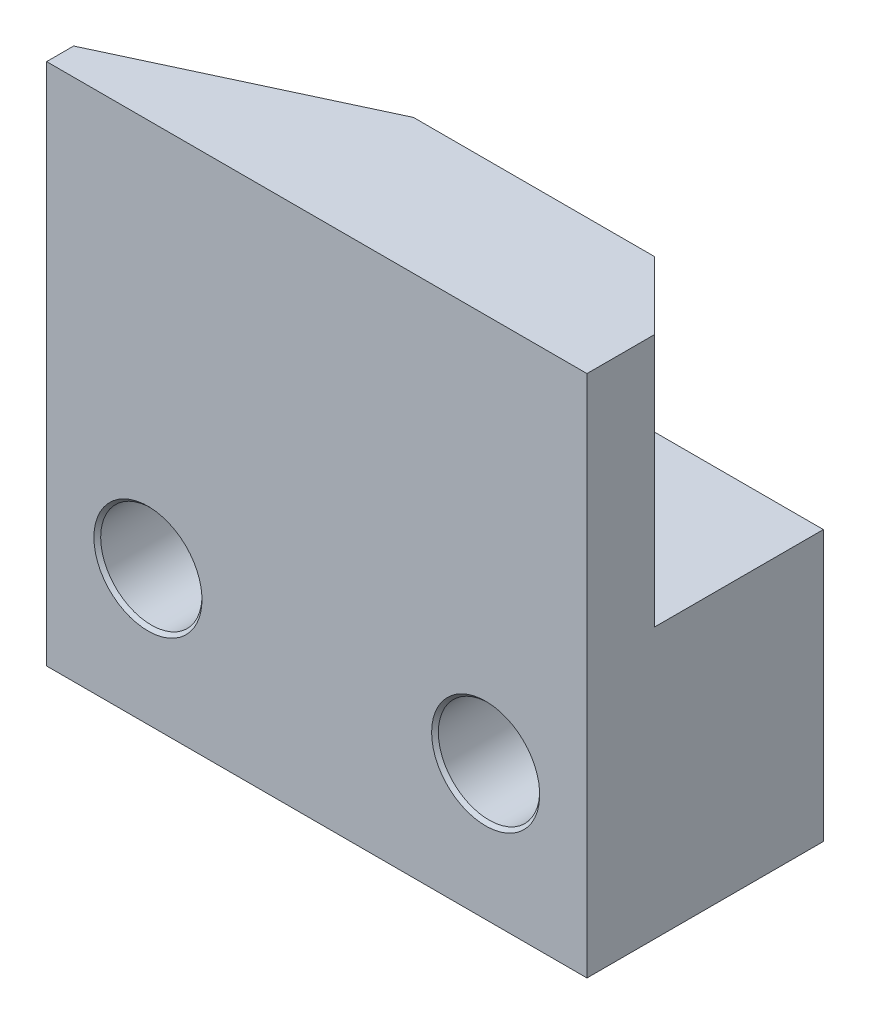
SolidWorks part; units mm, degrees
material "2024 Сплав"
ref_plane "Спереди" through (0, 0, 0) normal (0, 0, 1) x (1, 0, 0)
ref_plane "Сверху" through (0, 0, 0) normal (0, 1, 0) x (1, 0, 0)
ref_plane "Справа" through (0, 0, 0) normal (1, 0, 0) x (0, 0, -1)
sketch "Эскиз1" plane through (0, 0, 0) normal (0, 1, 0) x (1, 0, 0)
  line L0 (0, 0) -> (16, 0)
  line L1 (16, 0) -> (16, 7)
  line L2 (16, 7) -> (0, 7)
  line L3 (0, 7) -> (0, 0)
  dimension "D1" = 7
  dimension "D2" = 16
extrude "Бобышка-Вытянуть1" add sketch "Эскиз1" along normal blind 15.5
sketch "Эскиз2" plane through (0, 15.5, 0) normal (0, 1, 0) x (1, 0, 0)
  line L0 (0, 0.8) -> (6.8624, 4)
  line L1 (0, 7) -> (0, 0) construction
  line L2 (6.8624, 4) -> (14, 4)
  line L3 (16, 0) -> (16, 7) construction
  line L4 (0, 0) -> (16, 0) construction
  line L5 (16, 7) -> (0, 7) construction
  line L6 (14, 4) -> (16, 2)
  line M1 (0, 7) -> (0, 0)
  line M3 (16, 0) -> (16, 7)
  line M4 (16, 7) -> (0, 7)
  dimension "D1" = 4
  dimension "D2" = 25
  dimension "D3" = 0.8
  dimension "D4" = 45
  dimension "D5" = 2
extrude "Вырез-Вытянуть1" cut sketch "Эскиз2" against normal offset from surface (7.5 mm away) 8 contours L0 L2 M3 M4 M1 up to face at (8, 0, -3.5)
hole_wizard "Отверстие обработанное метчиком M3x0.51" positions "Эскиз4" profile "Эскиз3" tap size "M3x0.5" standard "Ansi (метрические)" end condition through all
sketch "Эскиз4" plane through (0, 0, -7) normal (0, 0, -1) x (-1, 0, 0)
  line L1 (0, 8) -> (0, 0) construction
  line L2 (0, 8) -> (-16, 8) construction
  point P0 (-3, 4)
  point P1 (-13, 4)
  dimension "D1" = 4
  dimension "D2" = 10
  dimension "D3" = 3
sketch "Эскиз3" plane through (3, 4, -7) normal (1, 0, 0) x (0, 1, 0)
  line L0 (0, 0) -> (0, 7)
  line L1 (0, 7) -> (1.6, 7)
  line L2 (1.5, 6.9) -> (1.5, 0.1)
  line L3 (1.5, 0.1) -> (1.6, 0)
  line L5 (1.6, 0) -> (0, 0)
  line L6 (-1.5, 0.1) -> (-1.6, 0) construction
  line L7 (1.6, 7) -> (1.5, 6.9)
  line L8 (-1.6, 7) -> (-1.5, 6.9) construction
  line L11 (0, -6.35) -> (0, 107.95) construction
  dimension "Диаметр резьбы" = 3
  dimension "Глубина проходного сверла" = 7
  dimension "Диаметр передней зенковки" = 3.2
  dimension "Угол передней зенковки" = 90
  dimension "Диаметр задней зенковки" = 3.2
  dimension "Угол задней зенковки" = 90
